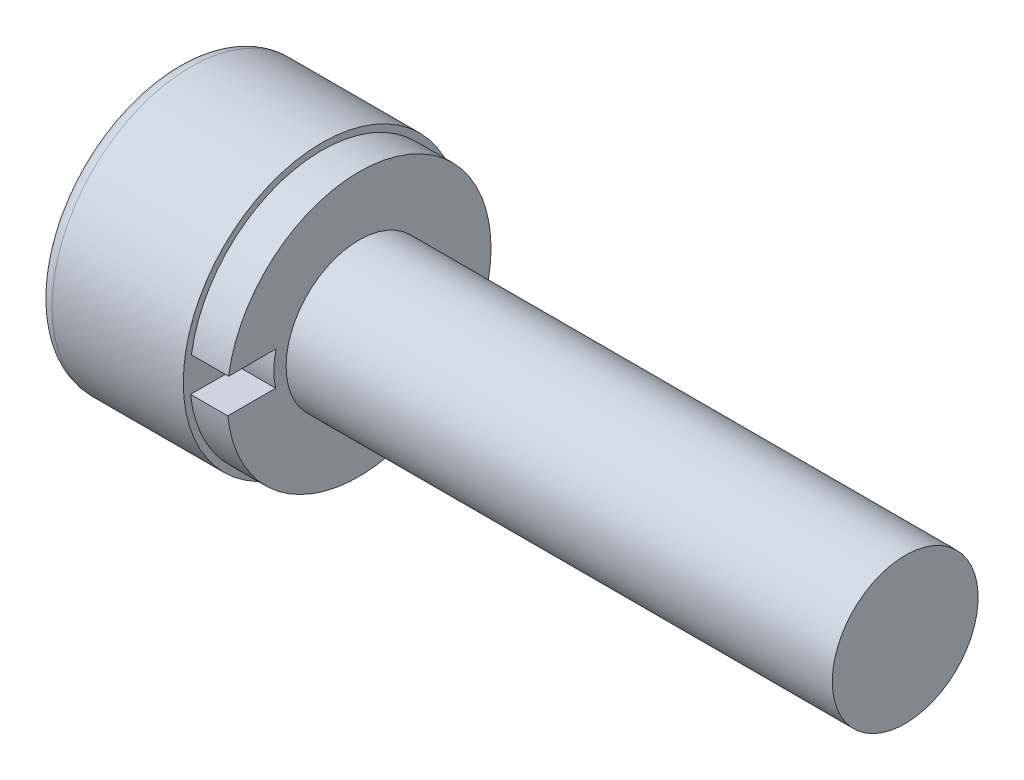
SolidWorks part; units mm, degrees
material "AISI 304"
ref_plane "前视基准面" through (0, 0, 0) normal (0, 0, 1) x (1, 0, 0)
ref_plane "上视基准面" through (0, 0, 0) normal (0, 1, 0) x (1, 0, 0)
ref_plane "右视基准面" through (0, 0, 0) normal (1, 0, 0) x (0, 0, -1)
sketch "草图1" plane through (0, 0, 0) normal (0, 0, 1) x (1, 0, 0)
  line L0 (0, 0) -> (17.0533, 0) construction
  line L1 (0, 0) -> (0, 1.9)
  line L2 (0, 1.9) -> (2, 1.9)
  line L3 (2, 1.9) -> (2, 1.81)
  line L4 (2, 1.81) -> (2.51, 1.81)
  line L5 (2.51, 1.81) -> (2.51, 1)
  line L6 (2.51, 1) -> (10, 1)
  line L7 (10, 1) -> (10, 0)
  line L8 (10, 0) -> (0, 0)
  dimension "D1" = 3.8
  dimension "D2" = 2
  dimension "D3" = 2
  dimension "D4" = 3.62
  dimension "D5" = 0.51
  dimension "长度" = 8
revolve "旋转1" add sketch "草图1" angle 360 about L0
sketch "草图2" plane through (0, 0, 0) normal (-1, 0, 0) x (0, 0, 1)
  line L1 (0.5105, -0.7279) -> (0.8857, 0.0782)
  line L2 (0.8857, 0.0782) -> (0.3751, 0.8061)
  line L3 (0.3751, 0.8061) -> (-0.5105, 0.7279)
  line L4 (-0.5105, 0.7279) -> (-0.8857, -0.0782)
  line L5 (-0.8857, -0.0782) -> (-0.3751, -0.8061)
  line L6 (-0.3751, -0.8061) -> (0.5105, -0.7279)
  circle A0 centre (0, 0) radius 0.77 construction
  dimension "D1" = 1.54
extrude "切除-拉伸1" cut sketch "草图2" against normal blind 1
fillet "圆角1" radius 0.2 1 edges at (0, 0, 1.9)
sketch "草图3" plane through (2.51, 0, 0) normal (1, 0, 0) x (0, 0, -1)
  line L0 (-1.1389, 0.2758) -> (-1.7889, 0.2758)
  line L1 (-1.8002, -0.1885) -> (-1.1431, -0.1885)
  circle A1 centre (0, 0) radius 1.81 construction
  circle A2 centre (0, 0) radius 1.81 construction
  circle A4 centre (0, 0) radius 1.81
  arc A5 (-1.7889, 0.2758) -> (-1.8002, -0.1885) centre (0, 0) ccw
  arc A6 (-1.1389, 0.2758) -> (-1.1431, -0.1885) centre (-0.1684, 0.0349) ccw
  dimension "D1" = 0
extrude "切除-拉伸2" cut sketch "草图3" against normal up to surface (0.51 mm away) up to face at (2, 0, 1.9)
